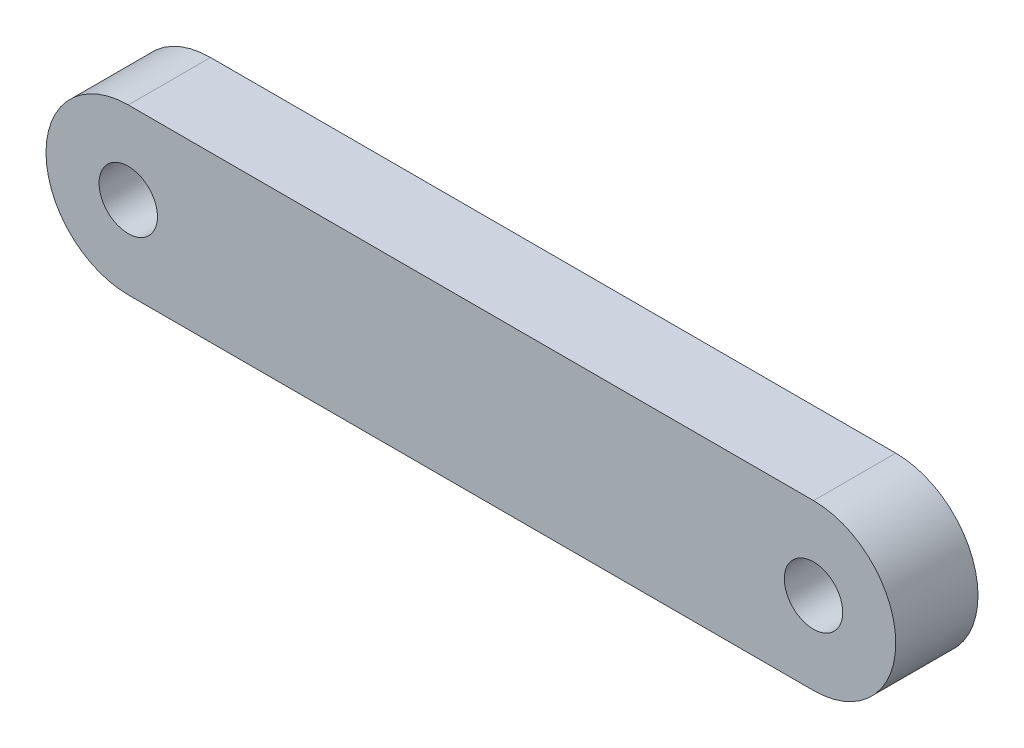
SolidWorks part; units mm, degrees
ref_plane "Front Plane" through (0, 0, 0) normal (0, 0, 1) x (1, 0, 0)
ref_plane "Top Plane" through (0, 0, 0) normal (0, 1, 0) x (1, 0, 0)
ref_plane "Right Plane" through (0, 0, 0) normal (1, 0, 0) x (0, 0, -1)
sketch "Sketch1" plane through (0, 0, 0) normal (0, 0, 1) x (1, 0, 0)
  line L0 (-10.415, 0) -> (10.415, 0) construction
  line L1 (-10.415, 2.5) -> (10.415, 2.5)
  line L2 (-10.415, -2.5) -> (10.415, -2.5)
  arc A0 (-10.415, 2.5) -> (-10.415, -2.5) centre (-10.415, 0) ccw
  arc A1 (10.415, -2.5) -> (10.415, 2.5) centre (10.415, 0) ccw
  circle A2 centre (-10.415, 0) radius 0.8875
  circle A3 centre (10.415, 0) radius 0.8875
  point P2 (0, 0)
  dimension "D2" = 2.5
  dimension "D3" = 1.775
  dimension "D1" = 20.83
extrude "Boss-Extrude1" add sketch "Sketch1" along normal blind 2.5
